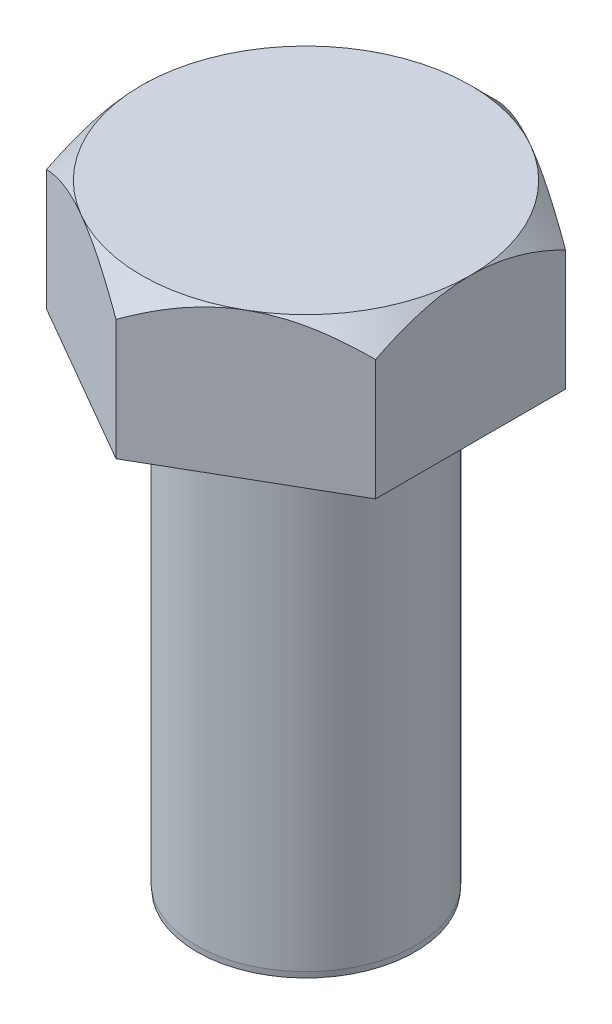
SolidWorks part; units mm, degrees
ref_plane "Front Plane" through (0, 0, 0) normal (0, 0, 1) x (1, 0, 0)
ref_plane "Top Plane" through (0, 0, 0) normal (0, 1, 0) x (1, 0, 0)
ref_plane "Right Plane" through (0, 0, 0) normal (1, 0, 0) x (0, 0, -1)
sketch "Sketch1" plane through (0, 0, 0) normal (0, 1, 0) x (1, 0, 0)
  line L1 (0, 8.2562) -> (-7.1501, 4.1281)
  line L2 (-7.1501, 4.1281) -> (-7.1501, -4.1281)
  line L3 (-7.1501, -4.1281) -> (0, -8.2562)
  line L4 (0, -8.2562) -> (7.1501, -4.1281)
  line L5 (7.1501, -4.1281) -> (7.1501, 4.1281)
  line L6 (7.1501, 4.1281) -> (0, 8.2562)
  circle A0 centre (0, 0) radius 7.1501 construction
  dimension "D1" = 14.3002
extrude "Boss-Extrude1" add sketch "Sketch1" along normal blind 6.35
sketch "Sketch2" plane through (0, 0, 0) normal (0, -1, 0) x (1, 0, 0)
  circle A0 centre (0, 0) radius 4.7625
  dimension "D1" = 9.525
extrude "Boss-Extrude2" add sketch "Sketch2" along normal blind 20.32
cosmetic thread "Cosmetic Thread1" parameters "D2"=8.2652
sketch "Sketch3" plane through (0, 6.35, 0) normal (0, 1, 0) x (1, 0, 0)
  circle A0 centre (0, 0) radius 7.1501
extrude "Cut-Extrude1" cut sketch "Sketch3" against normal blind 20.32 draft 45 flip side to cut
chamfer "Chamfer1" distance 0.254 angle 5 1 edges at (0, -20.32, -4.7625)
